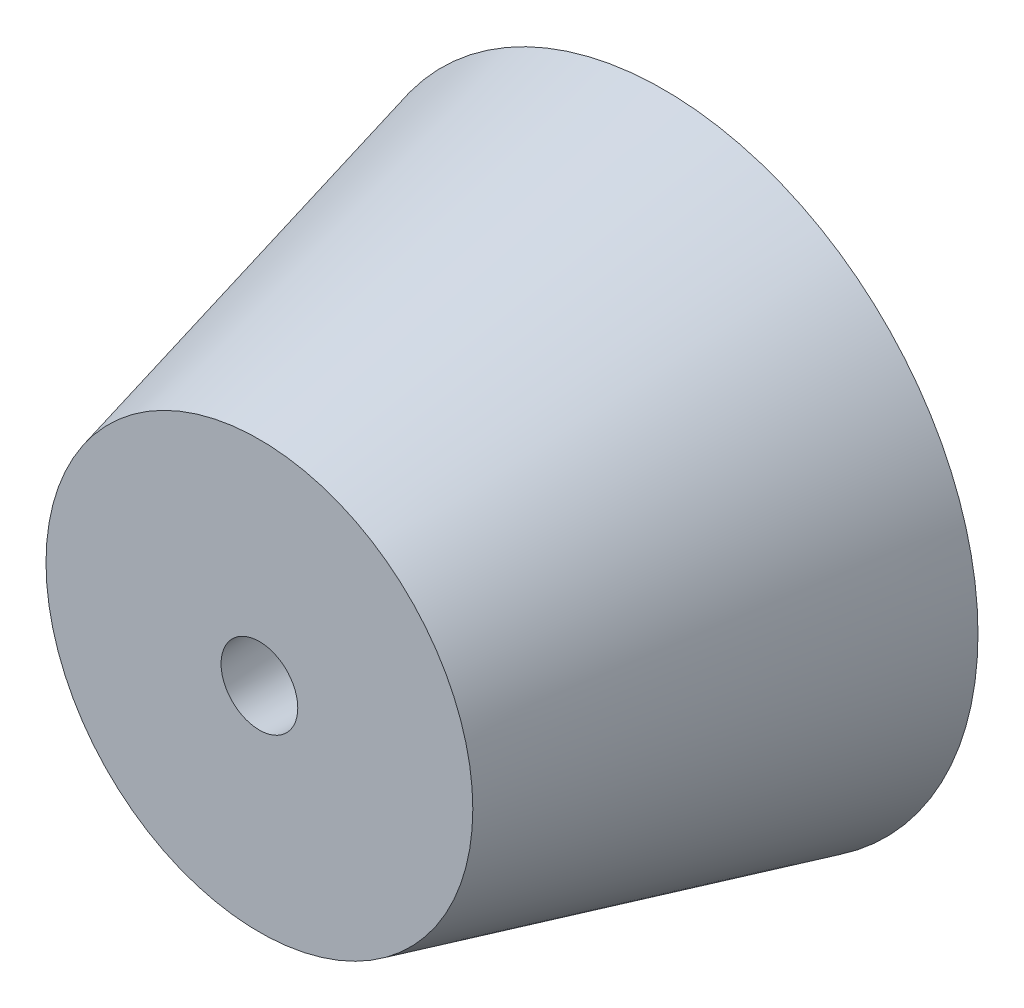
SolidWorks part; units mm, degrees
ref_plane "Alzado" through (0, 0, 0) normal (0, 0, 1) x (1, 0, 0)
ref_plane "Planta" through (0, 0, 0) normal (0, 1, 0) x (1, 0, 0)
ref_plane "Vista lateral" through (0, 0, 0) normal (1, 0, 0) x (0, 0, -1)
sketch "Croquis1" plane through (0, 0, 0) normal (0, 0, 1) x (1, 0, 0)
  circle A0 centre (0, 74.8005) radius 7.771
extrude "Saliente-Extruir1" add sketch "Croquis1" along normal blind 10 draft 14
sketch "Croquis2" plane through (0, 0, 0) normal (0, 0, -1) x (-1, 0, 0)
  circle A0 centre (0, 74.8005) radius 1.473
extrude "Cortar-Extruir1" cut sketch "Croquis2" against normal blind 13.8361 draft 3
